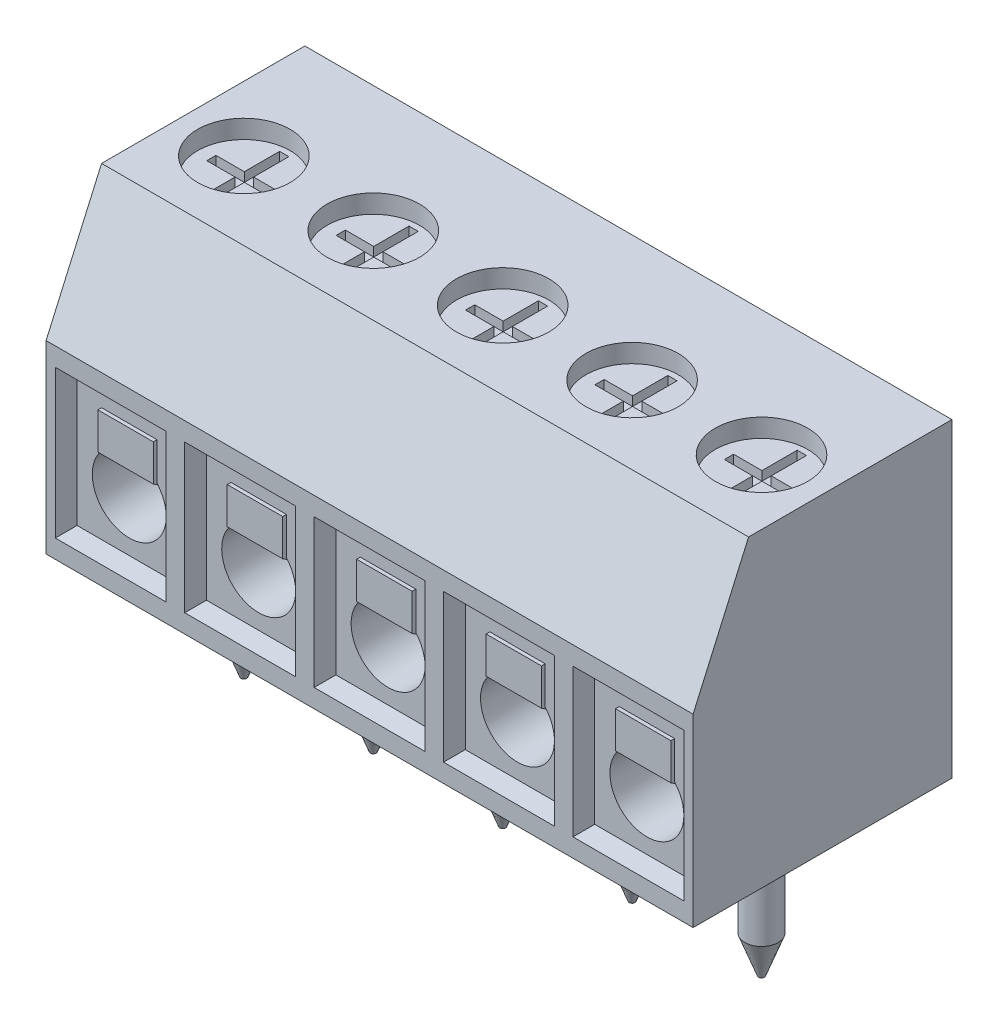
SolidWorks part; units mm, degrees
ref_plane "Front Plane" through (0, 0, 0) normal (0, 0, 1) x (1, 0, 0)
ref_plane "Top Plane" through (0, 0, 0) normal (0, 1, 0) x (1, 0, 0)
ref_plane "Right Plane" through (0, 0, 0) normal (1, 0, 0) x (0, 0, -1)
sketch "Sketch1" plane through (0, 0, 0) normal (1, 0, 0) x (0, 0, -1)
  line L0 (0, 5) -> (1.5, 8.4)
  line L1 (0, 0) -> (7, 0)
  line L2 (0, 0) -> (0, 5)
  line L3 (1.5, 8.4) -> (7, 8.4)
  line L4 (7, 0) -> (7, 8.4)
  dimension "D1" = 7
  dimension "D2" = 8.4
  dimension "D3" = 5
  dimension "D4" = 5.5
extrude "Boss-Extrude1" add sketch "Sketch1" along normal blind 17.5 contours L0 L3 L4 L1 L2
sketch "Sketch2" plane through (0, 8.4, 0) normal (0, 1, 0) x (1, 0, 0)
  line L0 (17.5, 7) -> (0, 7) construction
  line L1 (0, 1.5) -> (0, 7) construction
  circle A0 centre (1.75, 3.6) radius 1.25
  dimension "D1" = 2.5
  dimension "D2" = 3.4
  dimension "D3" = 1.75
extrude "Cut-Extrude1" cut sketch "Sketch2" against normal blind 0.5
sketch "Sketch3" plane through (0, 0, 0) normal (0, 0, 1) x (1, 0, 0)
  line L0 (0, 0) -> (0, 5) construction
  line L1 (0.25, 0.5) -> (3.25, 0.5)
  line L2 (0.25, 0.5) -> (0.25, 4.5)
  line L3 (0.25, 4.5) -> (3.25, 4.5)
  line L4 (3.25, 0.5) -> (3.25, 4.5)
  line L5 (17.5, 0) -> (0, 0) construction
  line L6 (17.5, 5) -> (0, 5) construction
  dimension "D1" = 0.25
  dimension "D2" = 3
  dimension "D3" = 0.5
  dimension "D4" = 0.5
extrude "Cut-Extrude2" cut sketch "Sketch3" against normal blind 0.5 draft 10 contours L3 L4 L1 L2
sketch "Sketch4" plane through (0, 0, -0.5) normal (0, 0, 1) x (1, 0, 0)
  line L0 (1.75, 0.5882) -> (1.75, 4.4118) construction
  line L1 (0.3382, 0.5882) -> (3.1618, 0.5882) construction
  line L2 (0.3382, 4.4118) -> (3.1618, 4.4118) construction
  line L3 (0.25, 0.5) -> (3.25, 0.5) construction
  circle A0 centre (1.75, 2) radius 1
  point P8 (1.75, 0.5)
  dimension "D1" = 2
  dimension "D2" = 1.5
extrude "Cut-Extrude3" cut sketch "Sketch4" against normal blind 6
ref_plane "Plane1" through (1.75, 0, 0) normal (1, 0, 0) x (0, 0, -1)
sketch "Sketch6" plane through (0, 0, 0) normal (0, -1, 0) x (1, 0, 0)
  line L0 (1.75, -3.85) -> (1.75, 3.85) construction
  line L1 (17.5, -7) -> (0, -7) construction
  circle A0 centre (1.75, -3.6) radius 0.45
  dimension "D1" = 0.9
  dimension "D2" = 3.4
extrude "Boss-Extrude3" add sketch "Sketch6" along normal blind 3.8
chamfer "Chamfer1" distance 1 angle 20.4 1 edges at (1.75, -3.8, -4.05)
sketch "Sketch7" plane through (1.75, 0, 0) normal (1, 0, 0) x (0, 0, -1)
  line L0 (0.5, 3.6787) -> (0.5, 2.7432)
  line L1 (0.5, 0.5882) -> (0.5, 4.4118) construction
  line L2 (0.5, 2.7432) -> (1.8997, 1.8322)
  line L3 (1.8997, 1.8322) -> (5.8881, 1.4383)
extrude "Extrude-Thin1" add sketch "Sketch7" along normal mid plane 1.5 thin
sketch "Sketch8" plane through (0, 7.9, 0) normal (0, 1, 0) x (1, 0, 0)
  line L0 (1.75, 4.6908) -> (1.75, 2.5325)
  line L1 (1.75, -3.85) -> (1.75, 3.85) construction
  line L2 (0.858, 3.6116) -> (2.7323, 3.6116)
extrude "Cut-Extrude-Thin1" cut sketch "Sketch8" against normal mid plane 0.5 thin thin type mid plane wall 0.25
pattern_linear "LPattern1" count 5 spacing 3.5 along (1, 0, 0) of "Cut-Extrude1", "Cut-Extrude2", "Cut-Extrude3", "Boss-Extrude3", "Chamfer1", "Extrude-Thin1", "Cut-Extrude-Thin1"
ref_plane "Plane2" through (0, 8.4, -1.5) normal (-1, 0, 0) x (0, 0, 1)
